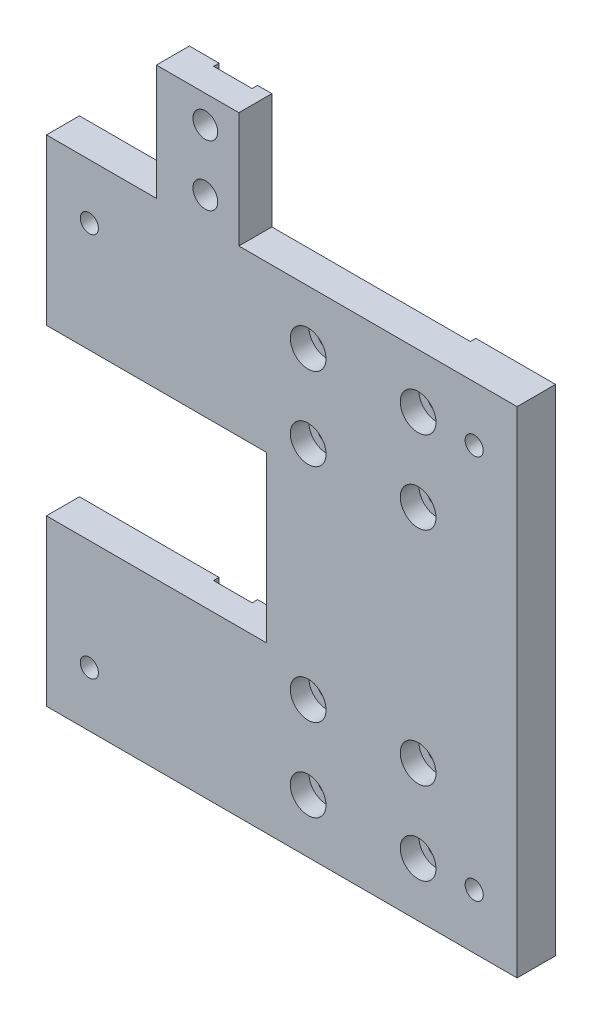
SolidWorks part; units mm, degrees
ref_plane "前视基准面" through (0, 0, 0) normal (0, 0, 1) x (1, 0, 0)
ref_plane "上视基准面" through (0, 0, 0) normal (0, 1, 0) x (1, 0, 0)
ref_plane "右视基准面" through (0, 0, 0) normal (1, 0, 0) x (0, 0, -1)
sketch "草图1" plane through (0, 0, 0) normal (0, 0, 1) x (1, 0, 0)
  line L1 (0, 0) -> (85.6, 0)
  line L2 (0, 0) -> (0, 90)
  line L3 (0, 90) -> (85.6, 90)
  line L4 (85.6, 0) -> (85.6, 90)
  dimension "D1" = 90
  dimension "D2" = 85.6
extrude "凸台-拉伸1" add sketch "草图1" along normal blind 6
sketch "草图2" plane through (0, 0, 6) normal (0, 0, 1) x (1, 0, 0)
  line L0 (85.6, 45) -> (0, 45) construction
  line L1 (85.6, 0) -> (85.6, 90) construction
  line L2 (0, 90) -> (0, 0) construction
  line L4 (0, 60) -> (40, 60)
  line L5 (0, 60) -> (0, 30)
  line L6 (0, 30) -> (40, 30)
  line L7 (40, 60) -> (40, 30)
  dimension "D1" = 40
  dimension "D2" = 30
extrude "切除-拉伸1" cut sketch "草图2" against normal through all
sketch "草图3" plane through (0, 0, 0) normal (0, 0, -1) x (-1, 0, 0)
  line L0 (0, 0) -> (-85.6, 0) construction
  line L1 (-85.6, 90) -> (-71.1, 90)
  line L2 (-85.6, 90) -> (-85.6, 0)
  line L3 (-85.6, 0) -> (-71.1, 0)
  line L4 (-71.1, 90) -> (-71.1, 0)
  dimension "D1" = 14.5
extrude "凸台-拉伸2" add sketch "草图3" along normal blind 1
hole_wizard "M3 六角凹头螺钉的柱形沉头孔1" positions "草图4" profile "草图5" counterbore size "M3" standard "ISO" end condition through all
sketch "草图4" plane through (0, 0, 6) normal (0, 0, 1) x (1, 0, 0)
  point P0 (67.6, 65.15)
  point P3 (47.6, 65.15)
  point P6 (67.6, 80.15)
  point P9 (47.6, 80.15)
sketch "草图5" plane through (67.6, 65.15, 6) normal (1, 0, 0) x (0, -1, 0)
  line L0 (0, 0) -> (0, 7)
  line L1 (0, 7) -> (1.7, 7)
  line L3 (1.7, 7) -> (1.7, 3.4)
  line L4 (1.7, 3.4) -> (3.25, 3.4)
  line L5 (3.25, 3.4) -> (3.25, 0)
  line L7 (3.25, 0) -> (0, 0)
  line L11 (0, -6.35) -> (0, 107.95) construction
  dimension "通孔孔直径" = 3.4
  dimension "通孔孔深度" = 7
  dimension "柱形沉头孔直径" = 6.5
  dimension "柱形沉头孔深度" = 3.4
ref_plane "基准面1" through (0, 45, 0) normal (0, 1, 0) x (1, 0, 0)
mirror "镜向1" about plane through (0, 45, 0) normal (0, 1, 0) of "M3 六角凹头螺钉的柱形沉头孔1"
hole_wizard "M4 螺纹孔1" positions "草图6" profile "草图7" tap size "M4" standard "ISO" end condition through all
sketch "草图6" plane through (0, 0, 6) normal (0, 0, 1) x (1, 0, 0)
  point P0 (77.8, 10)
  point P3 (7.8, 10)
  point P6 (77.8, 80)
  point P9 (7.8, 80)
sketch "草图7" plane through (77.8, 10, 6) normal (1, 0, 0) x (0, -1, 0)
  line L0 (0, 0) -> (0, 7)
  line L1 (0, 7) -> (1.65, 7)
  line L2 (1.65, 7) -> (1.65, 0)
  line L5 (1.65, 0) -> (0, 0)
  line L11 (0, -6.35) -> (0, 107.95) construction
  dimension "通孔螺纹孔钻头直径" = 3.3
  dimension "通孔螺纹孔钻头深度" = 7
cosmetic thread "孔螺蚊线1" parameters "D2"=4
cosmetic thread "孔螺蚊线2" parameters "D2"=4
cosmetic thread "孔螺蚊线3" parameters "D2"=4
cosmetic thread "孔螺蚊线4" parameters "D2"=4
sketch "草图11" plane through (0, 90, 0) normal (0, 1, 0) x (1, 0, 0)
  line L0 (85.6, -6) -> (0, -6) construction
  line L1 (0, 0) -> (35, 0)
  line L2 (0, 0) -> (0, -6)
  line L3 (0, -6) -> (35, -6)
  line L4 (35, 0) -> (35, -6)
  dimension "D1" = 35
extrude "凸台-拉伸3" add sketch "草图11" along normal blind 21
sketch "草图12" plane through (0, 0, 6) normal (0, 0, 1) x (1, 0, 0)
  line L0 (85.6, 90) -> (0, 90) construction
  line L1 (0, 111) -> (20, 111)
  line L2 (0, 111) -> (0, 90)
  line L3 (0, 90) -> (20, 90)
  line L4 (20, 111) -> (20, 90)
  line L5 (35, 111) -> (35, 90) construction
  dimension "D1" = 15
extrude "切除-拉伸3" cut sketch "草图12" against normal blind 21
sketch "草图14" plane through (0, 0, 0) normal (0, 0, -1) x (-1, 0, 0)
  line L0 (-35, 111) -> (-20, 111) construction
  line L1 (-32.4, 111) -> (-25.4, 111)
  line L2 (-32.4, 111) -> (-32.4, -5.3244)
  line L3 (-32.4, -5.3244) -> (-25.4, -5.3244)
  line L4 (-25.4, 111) -> (-25.4, -5.3244)
  line L5 (-35, 111) -> (-35, 90) construction
  dimension "D1" = 7
  dimension "D2" = 2.6
extrude "切除-拉伸4" cut sketch "草图14" against normal blind 1
sketch "草图17" plane through (0, 0, 6) normal (0, 0, 1) x (1, 0, 0)
  line L0 (35, 111) -> (35, 90) construction
  line L1 (20, 111) -> (35, 111) construction
  circle A0 centre (28.9, 106) radius 2.25
  circle A1 centre (28.9, 95) radius 2.25
  point P4 (0, 0)
  dimension "D2" = 4.5
  dimension "D3" = 4.5
  dimension "D1" = 11
  dimension "D4" = 6.1
  dimension "D5" = 5
extrude "切除-拉伸5" cut sketch "草图17" against normal through all
